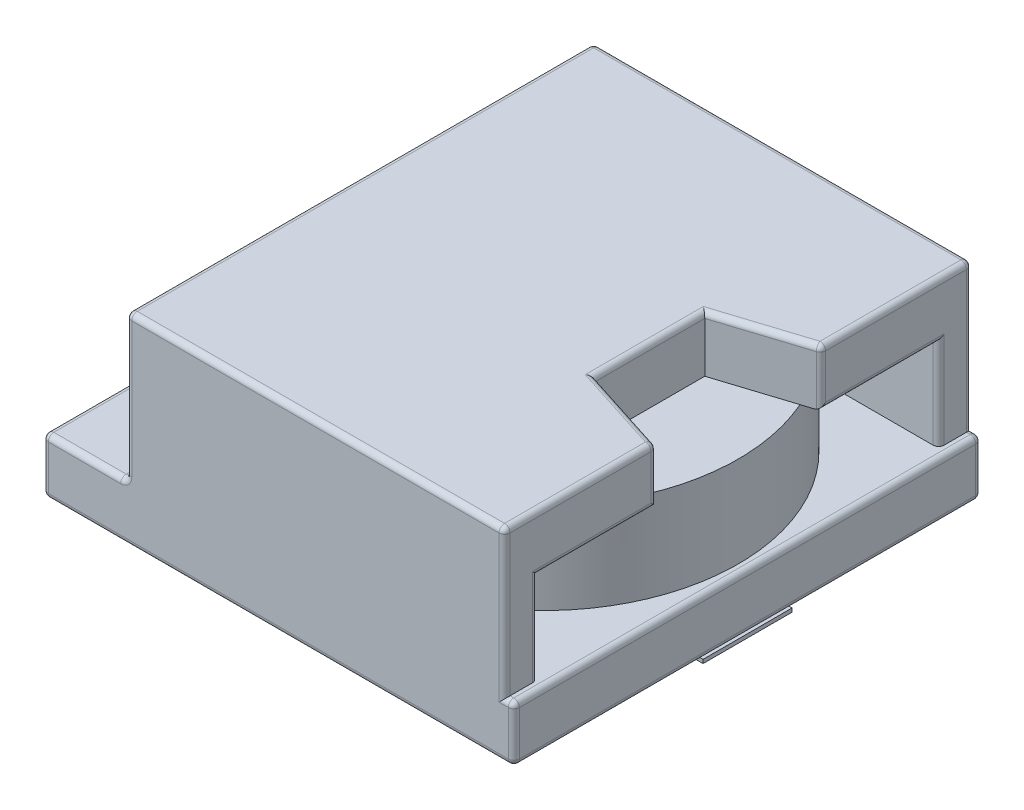
SolidWorks part; units mm, degrees
ref_plane "Front Plane" through (0, 0, 0) normal (0, 0, 1) x (1, 0, 0)
ref_plane "Top Plane" through (0, 0, 0) normal (0, 1, 0) x (1, 0, 0)
ref_plane "Right Plane" through (0, 0, 0) normal (1, 0, 0) x (0, 0, -1)
sketch "Sketch1" plane through (0, 0, 0) normal (0, 1, 0) x (1, 0, 0)
  line L1 (6.35, -6.3) -> (-6.35, -6.3)
  line L2 (6.35, -6.3) -> (6.35, 6.3)
  line L3 (6.35, 6.3) -> (-6.35, 6.3)
  line L4 (-6.35, -6.3) -> (-6.35, 6.3)
  line L5 (6.35, -6.3) -> (-6.35, 6.3) construction
  line L6 (6.35, 6.3) -> (-6.35, -6.3) construction
  point P0 (0, 0)
  dimension "D1" = 12.6
  dimension "D2" = 12.7
extrude "Boss-Extrude1" add sketch "Sketch1" along normal blind 1.5
sketch "Sketch2" plane through (0, 1.5, 0) normal (0, 1, 0) x (1, 0, 0)
  line L0 (-6.35, 0) -> (6.35, 0) construction
  line L1 (-6.35, 6.3) -> (-6.35, -6.3) construction
  line L2 (6.35, -6.3) -> (6.35, 6.3) construction
  line L3 (0.85, 6.3) -> (0.85, -6.3) construction
  line L4 (6.35, 6.3) -> (-6.35, 6.3) construction
  line L5 (-6.35, -6.3) -> (6.35, -6.3) construction
  circle A0 centre (0.85, 0) radius 5.25
  point P12 (0.85, 0)
  dimension "D2" = 10.5
  dimension "D1" = 5.5
extrude "Boss-Extrude2" add sketch "Sketch2" along normal blind 2.45 separate body contours A0
sketch "Sketch3" plane through (0, 1.5, 0) normal (0, 1, 0) x (1, 0, 0)
  line L0 (6.35, 6.3) -> (-6.35, 6.3) construction
  line L1 (-4.1, 6.3) -> (6.1, 6.3)
  line L2 (-4.1, 6.3) -> (-4.1, 5.4)
  line L3 (-4.1, 5.4) -> (6.1, 5.4)
  line L4 (6.1, 6.3) -> (6.1, 5.4)
  line L5 (-6.35, 0) -> (6.35, 0) construction
  line L6 (-6.35, 6.3) -> (-6.35, -6.3) construction
  line L7 (6.35, -6.3) -> (6.35, 6.3) construction
  line L8 (-4.1, -5.4) -> (6.1, -5.4)
  line L9 (6.1, -6.3) -> (6.1, -5.4)
  line L10 (-4.1, -6.3) -> (6.1, -6.3)
  line L11 (-4.1, -6.3) -> (-4.1, -5.4)
  line L12 (6.1, 6.8761) -> (6.1, -7.0324) construction
  line L13 (-4.4, 7.8064) -> (-4.4, -7.0324) construction
  circle A0 centre (0.85, 0) radius 5.25 construction
  point P16 (6.1, 0)
  point P17 (-4.4, 0)
  dimension "D1" = 0.9
  dimension "D2" = 0.3
extrude "Boss-Extrude3" add sketch "Sketch3" along normal blind 3.95
sketch "Sketch4" plane through (0, 5.45, 0) normal (0, 1, 0) x (1, 0, 0)
  line L1 (-4.1, 6.3) -> (6.1, 6.3)
  line L2 (-4.1, 6.3) -> (-4.1, -6.3)
  line L3 (-4.1, -6.3) -> (6.1, -6.3)
  line L4 (6.1, 6.3) -> (6.1, -6.3)
extrude "Boss-Extrude4" add sketch "Sketch4" against normal blind 1.5
sketch "Sketch5" plane through (0, 5.45, 0) normal (0, 1, 0) x (1, 0, 0)
  line L0 (-7.6361, 0) -> (8.2476, 0) construction
  line L1 (3.7147, -1.4817) -> (3.7147, 1.4817)
  line L2 (3.7147, 1.4817) -> (6.1, 2.2439)
  line L3 (6.1, -6.3) -> (6.1, 6.3) construction
  line L4 (6.1, 2.2439) -> (6.1, -2.2439)
  line L5 (3.7147, -1.4817) -> (6.1, -2.2439)
  point P3 (6.1, 2.6166)
  point P10 (6.1, 0)
  point P11 (3.7147, 0)
  point P12 (6.1, 2.4466)
  point P13 (3.7147, 1.4817)
  point P14 (6.1, 2.2439)
extrude "Cut-Extrude1" cut sketch "Sketch5" against normal blind 1.5
sketch "Sketch6" plane through (0, 0, 0) normal (0, -1, 0) x (1, 0, 0)
  line L0 (-8.6397, 0) -> (9.4251, 0) construction
  line L1 (-6.35, -2.2) -> (-4.55, -2.2)
  line L2 (-6.35, 5) -> (-4.55, 5)
  line L3 (-6.35, 5) -> (-6.35, 2.2)
  line L4 (-6.35, 2.2) -> (-4.55, 2.2)
  line L5 (-4.55, 5) -> (-4.55, 2.2)
  line L6 (-4.55, -5) -> (-4.55, -2.2)
  line L7 (-6.35, -5) -> (-4.55, -5)
  line L8 (-6.35, -5) -> (-6.35, -2.2)
  line L9 (6.35, 6.3) -> (6.35, -6.3) construction
  line L10 (6.35, 1.2) -> (4.75, 1.2)
  line L11 (6.35, 1.2) -> (6.35, -1.2)
  line L12 (6.35, -1.2) -> (4.75, -1.2)
  line L13 (4.75, 1.2) -> (4.75, -1.2)
  point P17 (4.75, 0)
  dimension "D1" = 4.4
  dimension "D2" = 2.8
  dimension "D3" = 1.8
  dimension "D4" = 9.3
  dimension "D5" = 1.6
  dimension "D6" = 2.4
extrude "Boss-Extrude5" add sketch "Sketch6" along normal blind 0.1 separate body
fillet "Fillet1" radius 0.15 34 edges at (1, 5.45, 6.3) (6.1, 5.45, 4.2719) (1, 5.45, -6.3) (6.1, 3.95, 3.8219) (-6.35, 0.75, 6.3) (0, 0, 6.3) (6.35, 0.75, -6.3) (0, 0, -6.3) (-4.1, 1.5, -5.85) (6.1, 2.725, -5.4) (-4.1, 1.5, 5.85) (6.1, 2.725, 5.4) (-5.225, 1.5, 6.3) (6.225, 1.5, 6.3) (6.35, 1.5, 0) (6.225, 1.5, -6.3) (-5.225, 1.5, -6.3) (-6.35, 1.5, 0) (-6.35, 0, 0) (-6.35, 0.75, -6.3) (6.35, 0, 0) (6.35, 0.75, 6.3) (6.1, 5.45, -4.2719) (6.1, 3.95, -3.8219) (6.1, 4.7, -2.2439) (6.1, 4.7, 2.2439) (4.9073, 5.45, -1.8628) (3.7147, 5.45, 0) (4.9073, 5.45, 1.8628) (-4.1, 3.475, 6.3) (-4.1, 3.475, -6.3) (6.1, 3.475, -6.3) (6.1, 3.475, 6.3) (-4.1, 5.45, 0)
